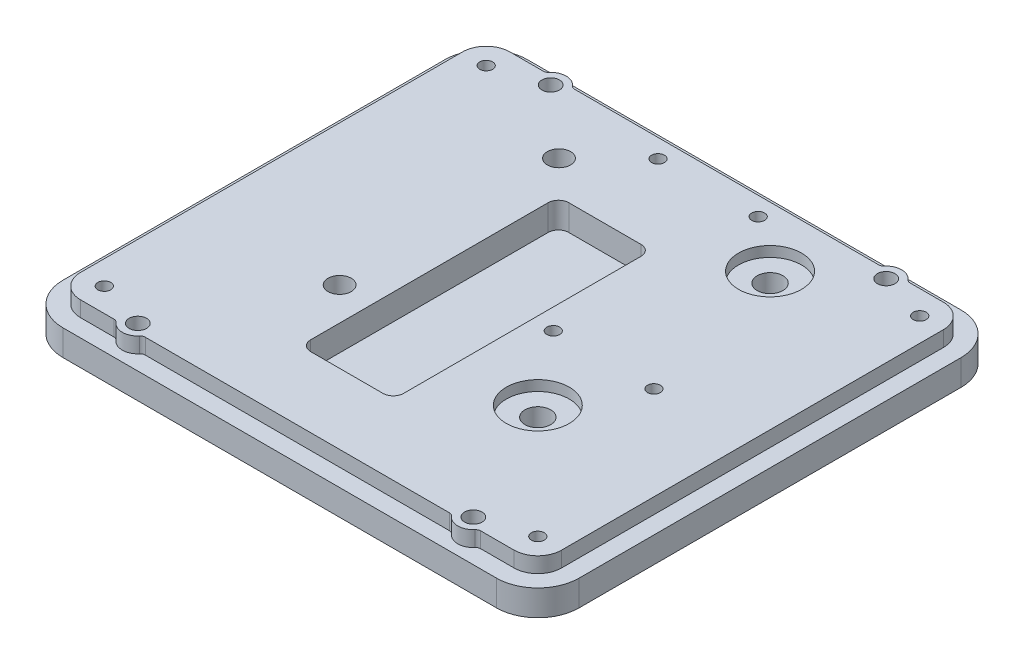
SolidWorks part; units mm, degrees
material "A5052"
ref_plane "Front Plane" through (0, 0, 0) normal (0, 0, 1) x (1, 0, 0)
ref_plane "Top Plane" through (0, 0, 0) normal (0, 1, 0) x (1, 0, 0)
ref_plane "Right Plane" through (0, 0, 0) normal (1, 0, 0) x (0, 0, -1)
sketch "Sketch1" plane through (0, 0, 0) normal (0, 1, 0) x (1, 0, 0)
  line L1 (-50, 45) -> (50, 45)
  line L2 (-50, 45) -> (-50, -45)
  line L3 (-50, -45) -> (50, -45)
  line L4 (50, 45) -> (50, -45)
  line L5 (-50, 45) -> (50, -45) construction
  line L6 (-50, -45) -> (50, 45) construction
  point P0 (0, 0)
  dimension "D1" = 100
  dimension "D2" = 90
extrude "Boss-Extrude1" add sketch "Sketch1" along normal blind 8
fillet "Fillet1" radius 8 4 edges at (50, 4, 45) (50, 4, -45) (-50, 4, -45) (-50, 4, 45)
sketch "Sketch6" plane through (0, 8, 0) normal (0, 1, 0) x (1, 0, 0)
  line L0 (20, 30) -> (20, -15) construction
  line L1 (-42, -45) -> (42, -45) construction
  line L2 (50, -37) -> (50, 37) construction
  circle A0 centre (20, 30) radius 6.1
  circle A1 centre (20, -15) radius 6.1
  dimension "D1" = 12.2
  dimension "D2" = 45
  dimension "D3" = 30
  dimension "D4" = 30
extrude "Cut-Extrude1" cut sketch "Sketch6" against normal blind 2
sketch "Sketch7" plane through (0, 8, 0) normal (0, 1, 0) x (1, 0, 0)
  line L4 (-42, -41.6) -> (42, -41.6)
  line L5 (-42, -41.6) -> (42, -41.6)
  line L6 (42, 41.6) -> (-42, 41.6)
  line L7 (42, 41.6) -> (-42, 41.6)
  line L24 (46.6, -37) -> (46.6, 37)
  line L26 (46.6, -37) -> (46.6, 37)
  line L30 (-46.6, 37) -> (-46.6, -37)
  line L31 (-46.6, 37) -> (-46.6, -37)
  arc A8 (42, -41.6) -> (46.6, -37) centre (42, -37) ccw
  arc A20 (42, -41.6) -> (46.6, -37) centre (42, -37) ccw
  arc A24 (46.6, 37) -> (42, 41.6) centre (42, 37) ccw
  arc A26 (46.6, 37) -> (42, 41.6) centre (42, 37) ccw
  arc A28 (-42, 41.6) -> (-46.6, 37) centre (-42, 37) ccw
  arc A29 (-42, 41.6) -> (-46.6, 37) centre (-42, 37) ccw
  arc A30 (-46.6, -37) -> (-42, -41.6) centre (-42, -37) ccw
  arc A31 (-46.6, -37) -> (-42, -41.6) centre (-42, -37) ccw
  dimension "D1" = 3.4
extrude "Cut-Extrude2" cut sketch "Sketch7" against normal blind 3 flip side to cut
hole_wizard "M3x0.5 Tapped Hole1" positions "Sketch8" profile "Sketch9" tap size "M3x0.5" standard "ANSI Metric" end condition through all
sketch "Sketch8" plane through (0, 8, 0) normal (0, 1, 0) x (1, 0, 0)
  line L4 (42, 45) -> (-42, 45) construction
  point P18 (-42, -37)
  point P21 (-42, 37)
  point P24 (42, 37)
  point P27 (42, -37)
  point P30 (-9.7, 38)
  point P33 (9.7, 38)
  point P48 (28.5, -1)
  point P51 (9, -1)
  dimension "D6" = 7
sketch "Sketch9" plane through (-42, 8, 37) normal (1, 0, 0) x (0, 0, 1)
  line L0 (0, 0) -> (0, 8)
  line L1 (0, 8) -> (1.25, 8)
  line L2 (1.25, 8) -> (1.25, 0)
  line L5 (1.25, 0) -> (0, 0)
  line L11 (0, -6.35) -> (0, 107.95) construction
  dimension "Thru Tap Drill Dia." = 2.5
  dimension "Thru Tap Drill Depth" = 8
cosmetic thread "Hole Thread15" parameters "D2"=3
cosmetic thread "Hole Thread18" parameters "D2"=3
cosmetic thread "Hole Thread29" parameters "D2"=3
cosmetic thread "Hole Thread30" parameters "D2"=3
cosmetic thread "Hole Thread36" parameters "D2"=3
cosmetic thread "Hole Thread39" parameters "D2"=3
cosmetic thread "Hole Thread43" parameters "D2"=3
cosmetic thread "Hole Thread44" parameters "D2"=3
hole_wizard "M6x1.0 Tapped Hole2" positions "Sketch10" profile "Sketch11" tap size "M6x1.0" standard "ANSI Metric" end condition through all
sketch "Sketch10" plane through (0, 8, 0) normal (0, 1, 0) x (1, 0, 0)
  point P0 (20, 30)
  point P3 (20, -15)
sketch "Sketch11" plane through (20, 8, -30) normal (1, 0, 0) x (0, 0, 1)
  line L0 (0, 0) -> (0, 8)
  line L1 (0, 8) -> (2.5, 8)
  line L2 (2.5, 8) -> (2.5, 0)
  line L5 (2.5, 0) -> (0, 0)
  line L11 (0, -6.35) -> (0, 107.95) construction
  dimension "Thru Tap Drill Dia." = 5
  dimension "Thru Tap Drill Depth" = 8
cosmetic thread "Hole Thread11" parameters "D2"=6
cosmetic thread "Hole Thread12" parameters "D2"=6
sketch "Sketch12" plane through (0, 8, 0) normal (0, 1, 0) x (1, 0, 0)
  line L0 (-32.5, 40) -> (32.5, 40) construction
  line L1 (32.5, 40) -> (32.5, -40) construction
  line L2 (32.5, -40) -> (-32.5, -40) construction
  line L3 (-32.5, -40) -> (-32.5, 40) construction
  line L4 (42, 45) -> (-42, 45) construction
  line L5 (-42, -45) -> (42, -45) construction
  line L6 (-50, 37) -> (-50, -37) construction
  line L7 (50, -37) -> (50, 37) construction
  circle A0 centre (-32.5, 40) radius 1.6608
  circle A1 centre (-32.5, 40) radius 3
  circle A3 centre (32.5, 40) radius 3
  circle A5 centre (-32.5, -40) radius 3
  circle A7 centre (32.5, -40) radius 3
  circle A8 centre (32.5, 40) radius 1.6608
  circle A9 centre (32.5, -40) radius 1.6608
  circle A10 centre (-32.5, -40) radius 1.6608
  dimension "D1" = 6
  dimension "D2" = 5
  dimension "D3" = 5
  dimension "D4" = 17.5
  dimension "D5" = 17.5
extrude "Boss-Extrude2" add sketch "Sketch12" against normal up to surface (3 mm away) up to face at (0, 5, 0)
hole_wizard "CBORE for M3 SHCS1" positions "Sketch13" profile "Sketch14" counterbore size "M3" standard "ANSI Metric" end condition through all
sketch "Sketch13" plane through (0, 0, 0) normal (0, -1, 0) x (-1, 0, 0)
  line L0 (-20, 30) -> (-20, -15) construction
  line L2 (-20, 7.5) -> (-77.5775, 7.5) construction
  point P0 (32.5, -40)
  point P3 (-32.5, -40)
  point P6 (32.5, 40)
  point P9 (-32.5, 40)
sketch "Sketch14" plane through (-32.5, 0, 40) normal (1, 0, 0) x (0, 0, -1)
  line L0 (0, 0) -> (0, 8)
  line L1 (0, 8) -> (1.7, 8)
  line L3 (1.7, 8) -> (1.7, 3)
  line L4 (1.7, 3) -> (3.25, 3)
  line L5 (3.25, 3) -> (3.25, 0)
  line L7 (3.25, 0) -> (0, 0)
  line L11 (0, -6.35) -> (0, 107.95) construction
  dimension "Thru Hole Dia." = 3.4
  dimension "Thru Hole Depth" = 8
  dimension "C'Bore Dia." = 6.5
  dimension "C'Bore Depth" = 3
fillet "Fillet2" radius 1 8 edges at (-35.0377, 6.5, -41.6) (-29.9623, 6.5, -41.6) (29.9623, 6.5, -41.6) (35.0377, 6.5, -41.6) (35.0377, 6.5, 41.6) (29.9623, 6.5, 41.6) (-29.9623, 6.5, 41.6) (-35.0377, 6.5, 41.6)
sketch "Sketch15" plane through (0, 8, 0) normal (0, 1, 0) x (1, 0, 0)
  line L1 (-13, 22) -> (5, 22)
  line L2 (-13, 22) -> (-13, -28)
  line L3 (-13, -28) -> (5, -28)
  line L4 (5, 22) -> (5, -28)
  line L5 (-50, 37) -> (-50, -37) construction
  line L6 (-42, -45) -> (42, -45) construction
  dimension "D1" = 18
  dimension "D2" = 50
  dimension "D3" = 17
  dimension "D4" = 37
extrude "Cut-Extrude3" cut sketch "Sketch15" against normal blind 5
fillet "Fillet3" radius 2 4 edges at (-13, 5.5, 28) (5, 5.5, 28) (5, 5.5, -22) (-13, 5.5, -22)
hole_wizard "CBORE for M4 SHCS1" positions "Sketch16" profile "Sketch17" counterbore size "M4" standard "ANSI Metric" end condition through all
sketch "Sketch16" plane through (0, 0, 0) normal (0, -1, 0) x (-1, 0, 0)
  point P0 (19.4, -14)
  point P3 (19.4, 28.5)
sketch "Sketch17" plane through (-19.4, 0, 14) normal (1, 0, 0) x (0, 0, -1)
  line L0 (0, 0) -> (0, 8)
  line L1 (0, 8) -> (2.25, 8)
  line L3 (2.25, 8) -> (2.25, 4)
  line L4 (2.25, 4) -> (4, 4)
  line L5 (4, 4) -> (4, 0)
  line L7 (4, 0) -> (0, 0)
  line L11 (0, -6.35) -> (0, 107.95) construction
  dimension "Thru Hole Dia." = 4.5
  dimension "Thru Hole Depth" = 8
  dimension "C'Bore Dia." = 8
  dimension "C'Bore Depth" = 4
